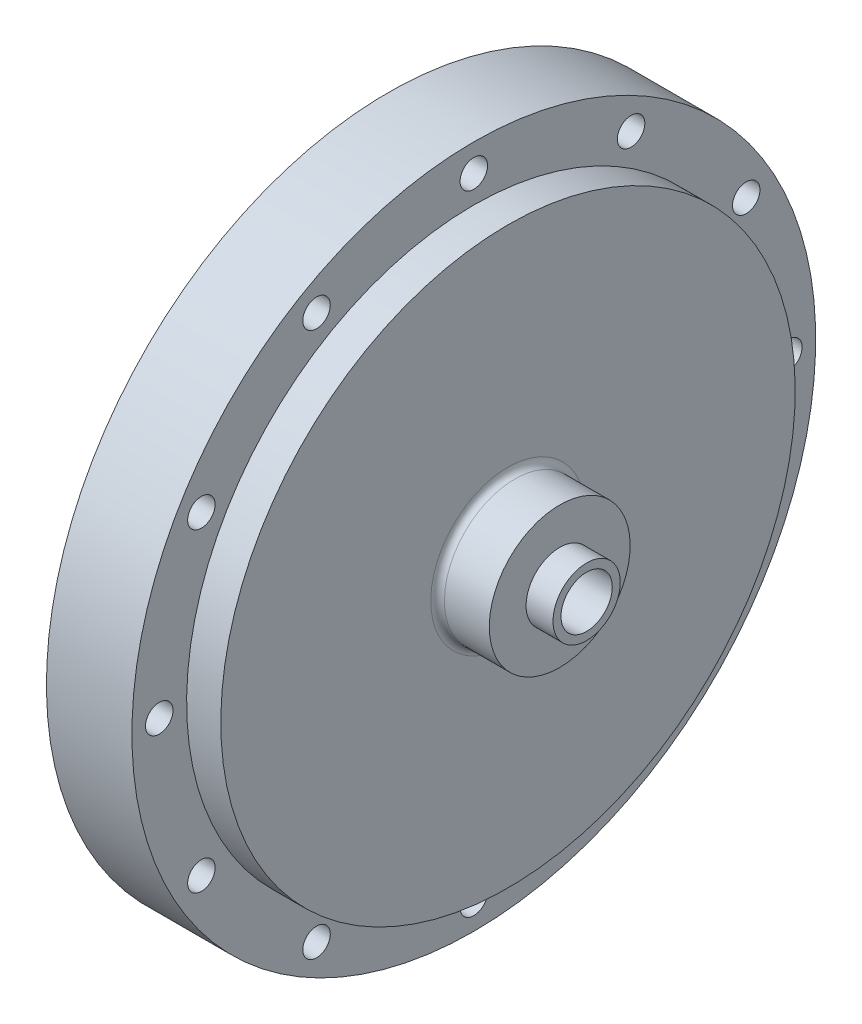
SolidWorks part; units mm, degrees
material "7075-T6 (SN)"
ref_plane "Front Plane" through (0, 0, 0) normal (0, 0, 1) x (1, 0, 0)
ref_plane "Top Plane" through (0, 0, 0) normal (0, 1, 0) x (1, 0, 0)
ref_plane "Right Plane" through (0, 0, 0) normal (1, 0, 0) x (0, 0, -1)
sketch "Sketch2" plane through (0, 0, 0) normal (0, 0, 1) x (1, 0, 0)
  line L0 (9.525, 0) -> (165.0115, 0) construction
  line L5 (41.355, 13.081) -> (41.355, 6.2484)
  line L6 (31.75, 13.081) -> (41.355, 13.081)
  line L7 (41.355, 6.2484) -> (46.355, 6.2484)
  line L8 (46.355, 6.2484) -> (46.355, 0)
  line L9 (9.525, 0) -> (46.355, 0)
  line L16 (9.525, 0) -> (9.525, 63.5)
  line L18 (31.75, 63.5) -> (31.75, 13.081)
  line L19 (31.75, 63.5) -> (9.525, 63.5)
  dimension "D1" = 63.5
  dimension "D2" = 36.83
  dimension "D4" = 13.081
  dimension "D5" = 22.225
  dimension "D7" = 6.2484
  dimension "D8" = 5
revolve "Main Structure" add sketch "Sketch2" angle 360 about L0
cosmetic thread "Cosmetic Thread1" parameters "D2"=23.1953
sketch "Sketch3" plane through (46.355, 0, 0) normal (1, 0, 0) x (0, 0, -1)
  circle A0 centre (0, 0) radius 4.7625
  dimension "D1" = 9.525
extrude "Oxidizer Inlet Hole" cut sketch "Sketch3" against normal through all
sketch "Sketch4" plane through (31.75, 0, 0) normal (-1, 0, 0) x (0, 0, 1)
  circle A0 centre (0, 0) radius 58.42 construction
  circle A1 centre (0, -58.42) radius 2.146
  circle A2 centre (-29.21, -50.5932) radius 2.146
  circle A3 centre (-50.5932, -29.21) radius 2.146
  circle A4 centre (-58.42, 0) radius 2.146
  circle A5 centre (-50.5932, 29.21) radius 2.146
  circle A6 centre (-29.21, 50.5932) radius 2.146
  circle A7 centre (0, 58.42) radius 2.146
  circle A8 centre (29.21, 50.5932) radius 2.146
  circle A9 centre (50.5932, 29.21) radius 2.146
  circle A10 centre (58.42, 0) radius 2.146
  circle A11 centre (50.5932, -29.21) radius 2.146
  circle A12 centre (29.21, -50.5932) radius 2.146
  point P29 (0, 0)
  dimension "D1" = 12
  dimension "D2" = 116.84
hole_wizard "Flange Holes" positions "Sketch7" profile "Sketch8" hole size "#7" standard "ANSI Inch" end condition up to next
sketch "Sketch7" plane through (31.75, 0, 0) normal (-1, 0, 0) x (0, 0, 1)
  point P0 (0, -58.42)
  point P3 (-29.21, -50.5932)
  point P6 (-50.5932, -29.21)
  point P9 (-58.42, 0)
  point P12 (-50.5932, 29.21)
  point P15 (-29.21, 50.5932)
  point P18 (0, 58.42)
  point P21 (29.21, 50.5932)
  point P24 (50.5932, 29.21)
  point P27 (58.42, 0)
  point P30 (50.5932, -29.21)
  point P33 (29.21, -50.5932)
sketch "Sketch8" plane through (31.75, -58.42, 0) normal (0, 1, 0) x (0, 0, -1)
  line L0 (0, 0) -> (0, 22.225)
  line L1 (0, 22.225) -> (2.5527, 22.225)
  line L2 (2.5527, 22.225) -> (2.5527, 0)
  line L5 (2.5527, 0) -> (0, 0)
  line L11 (0, -6.35) -> (0, 107.95) construction
  dimension "Thru Hole Dia." = 5.1054
  dimension "Thru Hole Depth" = 22.225
sketch "Sketch9" plane through (9.525, 0, 0) normal (-1, 0, 0) x (0, 0, 1)
  line L0 (0, 0) -> (-67.6727, 18.1329) construction
  line L1 (0, 0) -> (-58.42, 0) construction
  circle A0 centre (0, 0) radius 58.42 construction
  circle A1 centre (-56.4294, 15.1202) radius 2.9451
  circle A2 centre (56.4294, -15.1202) radius 2.9451
  point P14 (0, 0)
  dimension "D1" = 15
  dimension "D2" = 2
hole_wizard "Dowel Holes" positions "Sketch10" profile "Sketch11" hole size "3/16" standard "ANSI Inch"
sketch "Sketch10" plane through (9.525, 0, 0) normal (-1, 0, 0) x (0, 0, 1)
  point P0 (56.4294, -15.1202)
  point P3 (-56.4294, 15.1202)
sketch "Sketch11" plane through (9.525, -15.1202, 56.4294) normal (0, 1, 0) x (0, 0, 1)
  line L0 (0, 0) -> (0, 7.7808)
  line L1 (0, 7.7808) -> (2.3812, 6.35)
  line L2 (2.3812, 6.35) -> (2.3812, 0)
  line L5 (2.3812, 0) -> (0, 0)
  line L10 (0, 7.7808) -> (-2.3812, 6.35) construction
  line L11 (0, -6.35) -> (0, 107.95) construction
  dimension "Hole Dia." = 4.7625
  dimension "Hole Depth" = 6.35
  dimension "Drill Angle" = 118
sketch "Sketch12" plane through (9.525, 0, 0) normal (-1, 0, 0) x (0, 0, 1)
  circle A0 centre (0, 0) radius 28.575
  dimension "D1" = 57.15
extrude "Cut-Extrude2" cut sketch "Sketch12" against normal blind 9.525
ref_plane "Plane1" through (9.525, 0, 0) normal (-1, 0, 0) x (0, 0, 1)
ref_plane "Plane4" through (19.05, 0, 0) normal (-1, 0, 0) x (0, 0, 1)
sketch "Sketch16" plane through (19.05, 0, 0) normal (-1, 0, 0) x (0, 0, 1)
  circle A0 centre (0, 0) radius 28.575
  dimension "D1" = 57.15
ref_plane "Plane2" through (30.48, 0, 0) normal (-1, 0, 0) x (0, 0, 1)
sketch "Sketch17" plane through (30.48, 0, 0) normal (-1, 0, 0) x (0, 0, 1)
  circle A0 centre (0, 0) radius 4.7625
  dimension "D1" = 9.525
loft "Internal Flow Path Loft Cut" cut profiles "Sketch16", "Sketch17"
sketch "Sketch18" plane through (9.525, 0, 0) normal (-1, 0, 0) x (0, 0, 1)
  circle A0 centre (0, 0) radius 33.3375
  circle A1 centre (33.3375, 0) radius 1.5042
  dimension "D1" = 66.675
hole_wizard "#4-40 Tapped Hole1" positions "Sketch19" profile "Sketch20" tap size "#4-40" standard "ANSI Inch"
sketch "Sketch19" plane through (9.525, 0, 0) normal (-1, 0, 0) x (0, 0, 1)
  point P0 (33.3375, 0)
sketch "Sketch20" plane through (9.525, 0, 33.3375) normal (0, 1, 0) x (0, 0, 1)
  line L0 (0, 0) -> (0, 13.8872)
  line L1 (0, 13.8872) -> (1.1303, 13.208)
  line L2 (1.1303, 13.208) -> (1.1303, 0)
  line L5 (1.1303, 0) -> (0, 0)
  line L10 (0, 13.8872) -> (-1.1303, 13.208) construction
  line L11 (0, -6.35) -> (0, 107.95) construction
  dimension "Tap Drill Dia." = 2.2606
  dimension "Tap Drill Depth" = 13.208
  dimension "Drill Angle" = 118
cosmetic thread "Hole Thread1" parameters "D1"=9.398, "D2"=2.8448
pattern_circular "CirPattern1" count 8 over 360 about axis through (0, 0, 0) along (1, 0, 0) of "#4-40 Tapped Hole1"
fillet "Fillet1" radius 1.27 1 edges at (31.75, -13.081, 0)
sketch "Sketch23" plane through (9.525, 0, 0) normal (-1, 0, 0) x (0, 0, 1)
  circle A0 centre (0, 0) radius 44.45
  circle A1 centre (0, 0) radius 63.5
  dimension "D1" = 88.9
split line "Split Line5"
sketch "Sketch25" plane through (31.75, 0, 0) normal (1, 0, 0) x (0, 0, -1)
  circle A0 centre (0, 0) radius 53.34
  circle A1 centre (0, 0) radius 63.5 construction
  dimension "D1" = 10.16
extrude "Cut-Extrude3" cut sketch "Sketch25" against normal blind 6.35 flip side to cut
